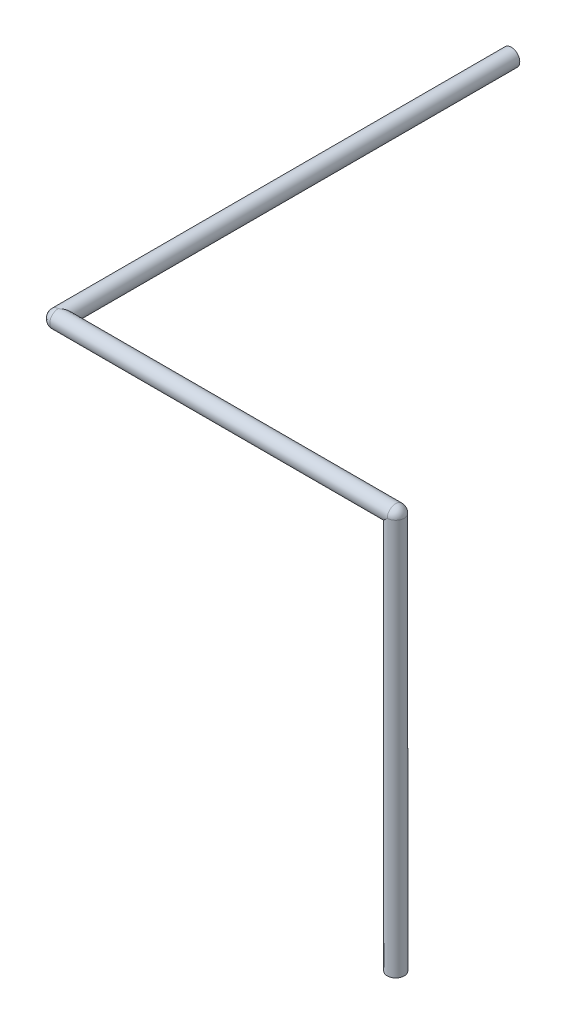
SolidWorks part; units mm, degrees
material "ABS PC"
ref_plane "Front" through (0, 0, 0) normal (0, 0, 1) x (1, 0, 0)
ref_plane "Top" through (0, 0, 0) normal (0, 1, 0) x (1, 0, 0)
ref_plane "Right" through (0, 0, 0) normal (1, 0, 0) x (0, 0, -1)
sketch "Sketch4" plane through (0, 0, 0) normal (0, 0, 1) x (1, 0, 0)
  circle A0 centre (0, 0) radius 1.905
  dimension "D1" = 3.81
extrude "Boss-Extrude1" add sketch "Sketch4" along normal blind 101.6
sketch "Sketch5" plane through (0, 0, 0) normal (1, 0, 0) x (0, 0, -1)
  line L0 (-101.6, 1.905) -> (-101.6, -1.905) construction
  circle A0 centre (-101.6, 0) radius 1.905
  point P2 (0, 0)
  dimension "D1" = 3.81
extrude "Boss-Extrude2" add sketch "Sketch5" along normal blind 75.692
sketch "Sketch6" plane through (0, 0, 0) normal (-1, 0, 0) x (0, 0, 1)
  line L0 (101.6, -1.905) -> (101.6, 1.905) construction
  line L1 (101.6, 1.905) -> (101.6, -1.905)
  arc A0 (101.6, 1.905) -> (101.6, -1.905) centre (101.6, 0) cw
  arc A1 (101.6, -1.905) -> (101.6, 1.905) centre (101.6, 0) ccw construction
revolve "Revolve1" add sketch "Sketch6" angle 360 about L1
sketch "Sketch7" plane through (0, 0, 0) normal (0, 1, 0) x (1, 0, 0)
  line L1 (75.692, -103.505) -> (75.692, -99.695) construction
  circle A0 centre (75.692, -101.6) radius 1.905
  point P2 (0, 0)
  dimension "D1" = 3.81
extrude "Boss-Extrude3" add sketch "Sketch7" against normal blind 88.9
sketch "Sketch8" plane through (0, 0, 0) normal (0, 1, 0) x (1, 0, 0)
  line L0 (75.692, -99.695) -> (75.692, -103.505) construction
  line L2 (75.692, -99.695) -> (75.692, -103.505)
  arc A0 (75.692, -99.695) -> (75.692, -103.505) centre (75.692, -101.6) cw
revolve "Revolve2" add sketch "Sketch8" angle 360 about L2
